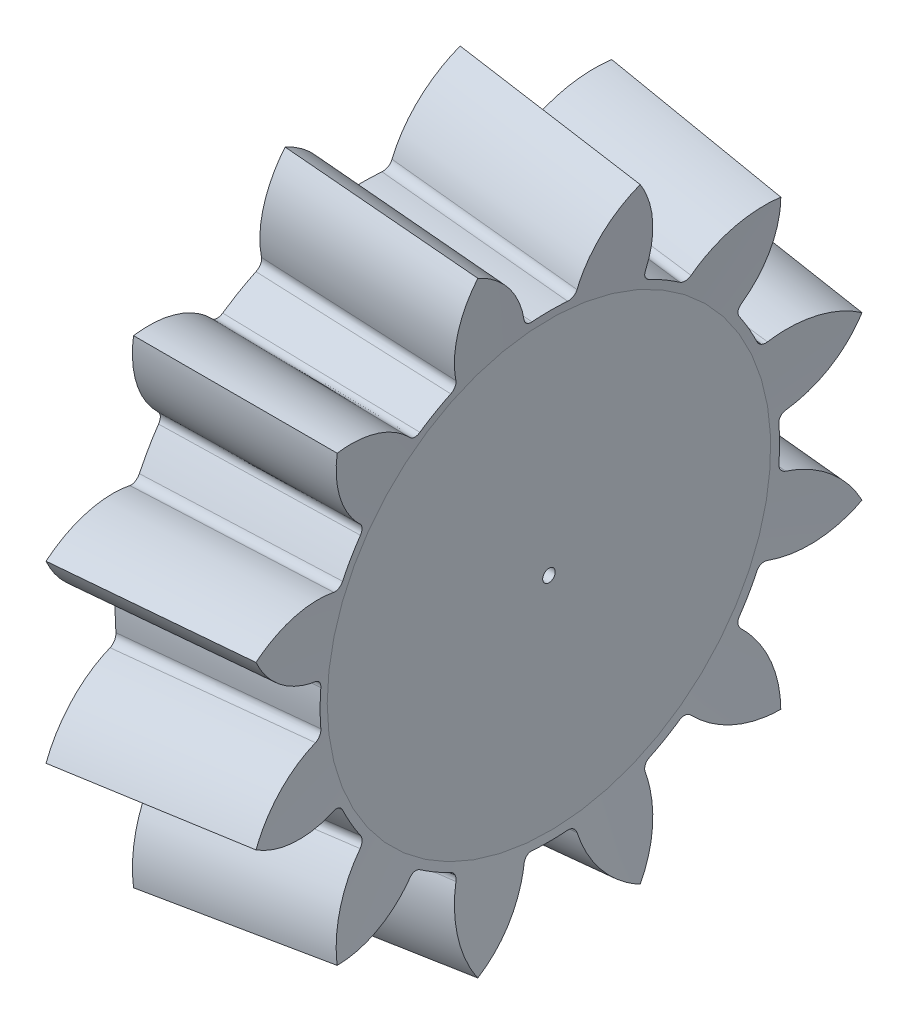
SolidWorks part; units mm, degrees
revolve "Base-Revolve" add sketch "BasProSke" angle 360 about L0
sketch "BasProSke" plane through (0, 0, 0) normal (0, 1, 0) x (1, 0, 0)
  line L0 (-10, 0) -> (60, 0) construction
  line L1 (0, 0) -> (0, 15.2645)
  line L2 (0, 0) -> (11.9508, 0)
  line L3 (11.9508, 0) -> (11.9508, 14.1609)
  line L4 (165.2984, 0) -> (-31.2241, 21.4388) construction
  line L5 (0, 15.2645) -> (0.7716, 22.3378)
  line L6 (165.2984, 0) -> (-7.6838, 23.4858) construction
  line L7 (165.2984, 0) -> (0, 15.2645) construction
  line L8 (0.7716, 22.3378) -> (12.6667, 20.7229)
  line L9 (12.6667, 20.7229) -> (11.9508, 14.1609)
  line L10 (0.2984, 18) -> (-11.6859, 18) construction
  dimension "Addendum" = 4.3636
  dimension "Pitch_rad" = 18
  dimension "Dedendum_plus" = 2.7518
  dimension "Face_wid" = 12
  dimension "Pitch_ang" = 6.226
  dimension "D1" = 30.5289
  dimension "D2" = 165.2984
  dimension "D3" = 165.9789
  dimension "D4" = 1.506
ref_plane "Plane1" through (0, 0, 0) normal (0, 0, 1) x (1, 0, 0)
ref_plane "Plane2" through (0, 0, 0) normal (0, 1, 0) x (1, 0, 0)
ref_plane "Plane3" through (0, 0, 0) normal (1, 0, 0) x (0, 0, -1)
sketch "HoldingSke" plane through (0, 0, 0) normal (0, 1, 0) x (1, 0, 0)
  line L0 (0, 0) -> (0.326, -0.0693)
  line L1 (-15, 0) -> (100, 0) construction
  line L2 (0, 0) -> (195.858, 55.667)
  line L3 (0, 0) -> (-11.863, 4.5341)
  line L4 (0, 0) -> (8.4473, 1.7955)
  line L5 (0, 0) -> (-9.3695, -3.4946)
  line L6 (0, 0) -> (-10.5278, -7.1032)
  line L7 (195.858, 55.667) -> (359.3705, 31.4336)
  line L8 (-76.2, 3) -> (-76.1, 3)
  line L9 (-71.009, 38.7566) -> (-53.1078, 45.2721)
  line L10 (-76.2, 71.12) -> (104.1128, 71.12)
  line L11 (0, 0) -> (-12, 0)
  line L12 (-76.2, 101.6) -> (-76.093, 101.6)
  line L13 (24.9733, 27.94) -> (52.9471, 28.6503)
  line L14 (24.9733, 27.94) -> (24.9743, 27.94)
  line L15 (24.9733, 27.94) -> (100.4124, 28.9058)
  line L16 (195.858, 55.667) -> (151.7007, -65.6542)
  circle A0 centre (0, 0) radius 0.4
  circle A1 centre (0, 0) radius 15.2645
  circle A2 centre (0, 0) radius 37.5
  circle A3 centre (0, 0) radius 0.4
  dimension "MHD" = 30.5289
  dimension "Hub_dia" = 75
  dimension "Bore" = 0.8
  dimension "MBD" = 0.8
  dimension "Num_teeth" = 12
  dimension "Pitch" = 0.3333
  dimension "Mounting_dist" = 10
  dimension "Show_teeth" = 12
  dimension "Thickness" = 12.7
  dimension "OAL" = 165.2985
  dimension "T_dim" = 0.1
  dimension "Ap" = 20
  dimension "H" = 19.05
  dimension "Pitch_radius" = 180.3128
  dimension "Width" = 12
  dimension "Backlash" = 0.107
  dimension "Addendum_fac" = 1.455
  dimension "Dedendum_fac" = 0.733
  dimension "Clearance_fac" = 0.188
  dimension "Dedendum_add" = 0.001
  dimension "Mating_teeth" = 110
  dimension "MnMD" = 165.2984
  dimension "Module" = 3
ref_plane "ToothPln" through (0.3858, 18.8011, 0) normal (-0.9941, 0.1084, 0) x (0, 0, -1)
ref_plane "ToothPln2" through (163.3544, -17.8205, 0) normal (-0.9941, 0.1084, 0) x (0, 0, 1)
sketch "TooCutSke" plane through (0.3858, 18.8011, 0) normal (-0.9941, 0.1084, 0) x (0, 0, -1)
  line L2 (0, 18.8059) -> (441.7526, -1629.8373) construction
  line L3 (0, 18.8059) -> (238.7007, -1753.2468) construction
  line L4 (0, -15.621) -> (0, 105.791) construction
  line L6 (-24.765, -3.5577) -> (21.082, -3.5577) construction
  line L7 (4.6587, 1.4192) -> (2.3833, 1.1127) construction
  arc A0 (-7.5403, -2.7227) -> (7.5403, -2.7227) centre (0, 18.8059) ccw
  arc A1 (-1.2274, 3.0551) -> (1.2274, 3.0551) centre (0, 18.8059) ccw
  circle A2 centre (0, 18.8059) radius 18 construction
  circle A3 centre (0, 18.8059) radius 16.9145 construction
  arc A4 (1.8196, 2.6281) -> (1.2274, 3.0551) centre (1.2712, 2.4918) ccw
  arc A5 (1.8196, 2.6281) -> (7.5403, -2.7227) centre (8.8069, 4.3651) ccw
  arc A6 (-7.5403, -2.7227) -> (-1.8196, 2.6281) centre (-8.8069, 4.3651) ccw
  arc A7 (-1.2274, 3.0551) -> (-1.8196, 2.6281) centre (-1.2712, 2.4918) ccw
  ellipse E0 centre (0, 18.6484) end of major axis (22.3378, 18.6484) minor radius 22.2061 construction
sketch "TooCutSke2" plane through (163.3544, -17.8205, 0) normal (-0.9941, 0.1084, 0) x (0, 0, 1)
  line L0 (0, 0) -> (0, 68.072) construction
  line L2 (21.082, 15.1744) -> (-20.32, 15.1744) construction
  circle A0 centre (0, 17.9262) radius 0.0127
  ellipse E1 centre (0, 0) end of major axis (-15.2645, 0) minor radius 15.1744 construction
  dimension "Dedendum_plus" = 2.7518
loft "ToothCut" cut profiles "TooCutSke2", "TooCutSke"
pattern_circular "TeethCuts" count 12 every 30 about axis through (-10, 0, 0) along (1, 0, 0) of "ToothCut"
sketch "HubSke" plane through (0, 0, 0) normal (-1, 0, 0) x (0, 0, 1)
  circle A0 centre (0, 0) radius 15.2645
  dimension "Diameter" = 30.5289
extrude "Hub" add sketch "HubSke" along normal blind 0.0001
sketch "BorSke" plane through (0, 0, 0) normal (1, 0, 0) x (0, 0, -1)
  circle A0 centre (0, 0) radius 0.4
  dimension "Diameter" = 0.8
extrude "Bore" cut sketch "BorSke" along normal mid plane 330.5969
sketch "KeySke" plane through (0, 0, 0) normal (1, 0, 0) x (0, 0, -1)
  line L0 (-0.05, 0) -> (-0.05, 0.5)
  line L1 (-0.05, 0.5) -> (0.05, 0.5)
  line L2 (0.05, 0.5) -> (0.05, 0)
  line L3 (0, 0) -> (0, 34) construction
  line L4 (-0.05, 0) -> (0.05, 0)
  dimension "Offset" = 0.5
extrude "Keyway" [suppressed] cut sketch "KeySke" along normal mid plane 330.5969
pattern_circular "Keyway2" [suppressed] count 2 every 90 about axis through (-10, 0, 0) along (1, 0, 0)
equation "' \"Module@HoldingSke\" = 6.35"
equation "' \"Num_teeth@HoldingSke\" = 12"
equation "' \"Mating_teeth@HoldingSke\" = 20"
equation "' \"Ap@HoldingSke\" =  20"
equation "' \"Ap@HoldingSke\" = 20"
equation "' \"Width@HoldingSke\" = 0.5 * 25.4"
equation "' \"Hub_dia@HoldingSke\"= 2 * 25.4"
equation "' \"Hub_dia@HoldingSke\" = 2 * 25.4"
equation "' \"Mounting_dist@HoldingSke\" = 3 * 25.4"
equation "' \"Bore@HoldingSke\" = 19"
equation "' \"T_dim@HoldingSke\" = 0.1 * 25.4"
equation "' \"Width@KeySke\" = 0.25 * 25.4"
equation "' \"Show_teeth@HoldingSke\" = 100"
equation "' \"Backlash@HoldingSke\" = 0.009 * 25.4"
equation "' \"Addendum_fac@HoldingSke\" = 1.0"
equation "' \"Dedendum_fac@HoldingSke\" = 1.188"
equation "' \"Dedendum_add@HoldingSke\" = 0.002 * 25.4"
equation "' \"Clearance_fac@HoldingSke\" = 0.188"
equation "\"Pitch@HoldingSke\" = 1 / \"Module@HoldingSke\""
equation "' \"Addendum_fac@HoldingSke\" = 0.54 + 0.46 / (\"Num_teeth@HoldingSke\" /  \"Mating_teeth@HoldingSke\" ) ^ 2"
equation " \"Addendum_fac@HoldingSke\" = 2 - (0.54 + 0.46 / (\"Mating_teeth@HoldingSke\" /  \"Num_teeth@HoldingSke\" ) ^ 2)"
equation "\"Dedendum_fac@HoldingSke\" = 2.188 - \"Addendum_fac@HoldingSke\""
equation "\"Pitch_rad@BasProSke\" = \"Num_teeth@HoldingSke\" / \"Pitch@HoldingSke\" / 2"
equation "\"Pitch_ang@BasProSke\" = atn(\"Num_teeth@HoldingSke\" / \"Mating_teeth@HoldingSke\") * (180 / 3.14159265)"
equation "\"Addendum@BasProSke\" = \"Addendum_fac@HoldingSke\" / \"Pitch@HoldingSke\""
equation "\"Dedendum_plus@BasProSke\" = (\"Dedendum_fac@HoldingSke\" / \"Pitch@HoldingSke\" + \"Dedendum_add@HoldingSke\") * 1.25"
equation "\"Face_wid@BasProSke\" = \"Width@HoldingSke\""
equation "\"Radius@TooCutSke\" = ((\"Num_teeth@HoldingSke\" + 2 * \"Addendum_fac@HoldingSke\") / \"Pitch@HoldingSke\" ) / 2"
equation "\"Overcut_dia@TooCutSke\" =  1.02 * (\"Num_teeth@HoldingSke\" + 2 * \"Addendum_fac@HoldingSke\") / \"Pitch@HoldingSke\""
equation "\"Pitch_dia@TooCutSke\" = \"Num_teeth@HoldingSke\" / \"Pitch@HoldingSke\""
equation "\"Base_dia@TooCutSke\" = \"Num_teeth@HoldingSke\" / \"Pitch@HoldingSke\" * cos((\"Ap@HoldingSke\"  * 3.14159265 / 180))"
equation "'  \"Root_dia@TooCutSke\" =  (\"Num_teeth@HoldingSke\" + 2) / \"Pitch@HoldingSke\" - 2 * (\"Addendum_fac@HoldingSke\" + \"Dedendum_fac@HoldingSke\") / \"Pitch@HoldingSke\" - \"Dedendum_add@HoldingSke\" * 2"
equation "'  \"Root_dia@TooCutSke\" = (\"Num_teeth@HoldingSke\" + 2) / \"Pitch@HoldingSke\" - 2 * (\"Addendum_fac@HoldingSke\" + \"Dedendum_fac@HoldingSke\") / \"Pitch@HoldingSke\" - \"Dedendum_add@HoldingSke\" * 2"
equation "\"Root_dia@TooCutSke\" =  \"Num_teeth@HoldingSke\" / \"Pitch@HoldingSke\" -  2 * \"Dedendum_fac@HoldingSke\" / \"Pitch@HoldingSke\" - \"Dedendum_add@HoldingSke\" * 2"
equation "\"Half_ang@TooCutSke\" = 180 / \"Num_teeth@HoldingSke\""
equation "\"Half_CT@TooCutSke\" = \"Num_teeth@HoldingSke\" / \"Pitch@HoldingSke\" * sin((3.14159265 / 2 / \"Num_teeth@HoldingSke\")) / 2 - 2 * \"Backlash@HoldingSke\" / 4"
equation "\"Flank_rad@TooCutSke\" = \"Num_teeth@HoldingSke\" / \"Pitch@HoldingSke\" / 5"
equation "\"Root_fillet@TooCutSke\" = \"Clearance_fac@HoldingSke\" / \"Pitch@HoldingSke\" + \"Dedendum_add@HoldingSke\""
equation "\"Offset@ToothPln2\"  = \"Num_teeth@HoldingSke\" / \"Pitch@HoldingSke\" / 2 / sin(atn(\"Num_teeth@HoldingSke\" / \"Mating_teeth@HoldingSke\"))"
equation "\"Dedendum_plus@TooCutSke2\" = \"Dedendum_plus@BasProSke\""
equation "\"MHD@HoldingSke\" = \"Num_teeth@HoldingSke\" / \"Pitch@HoldingSke\" - 2 * \"Dedendum_plus@BasProSke\" * cos(atn(\"Num_teeth@HoldingSke\" / \"Mating_teeth@HoldingSke\"))"
equation "\"MBD@HoldingSke\" = \"Num_teeth@HoldingSke\" / \"Pitch@HoldingSke\" - 2 * \"Dedendum_plus@BasProSke\" * cos(atn(\"Num_teeth@HoldingSke\" / \"Mating_teeth@HoldingSke\")) - 0.002 * 25.4"
equation "\"MnMD@HoldingSke\" =  \"Num_teeth@HoldingSke\" / \"Pitch@HoldingSke\" / 2 / (\"Num_teeth@HoldingSke\" / \"Mating_teeth@HoldingSke\") + \"Dedendum_plus@BasProSke\" * sin(atn(\"Num_teeth@HoldingSke\" / \"Mating_teeth@HoldingSke\"))"
equation "\"OAL@HoldingSke\" = \"MnMD@HoldingSke\""
equation "\"MHD@HoldingSke\" = ((sgn( \"MHD@HoldingSke\" - \"Hub_dia@HoldingSke\" )-1)*( \"MHD@HoldingSke\" - \"Hub_dia@HoldingSke\" ))/-2+ \"Hub_dia@HoldingSke\""
equation "\"MBD@HoldingSke\" = ((sgn( \"MBD@HoldingSke\" - \"Bore@HoldingSke\" )-1)*( \"MBD@HoldingSke\" - \"Bore@HoldingSke\" ))/-2+ \"Bore@HoldingSke\""
equation "\"Face_wid@BasProSke\" = ((sgn( \"Face_wid@BasProSke\" - \"Offset@ToothPln2\" * 0.9)-1)*( \"Face_wid@BasProSke\" - \"Offset@ToothPln2\" * 0.9))/-2+ \"Offset@ToothPln2\" * 0.9"
equation "\"OAL@HoldingSke\" = ((sgn( \"OAL@HoldingSke\" - \"Mounting_dist@HoldingSke\" )+1)*( \"OAL@HoldingSke\" - \"Mounting_dist@HoldingSke\" ))/2 + \"Mounting_dist@HoldingSke\" + 0.000002 * 25.4"
equation "\"Num_teeth@TeethCuts\" = int( \"Show_teeth@HoldingSke\" ) + 1"
equation "\"Num_teeth@TeethCuts\" = ((sgn( \"Num_teeth@TeethCuts\" - \"Num_teeth@HoldingSke\" )-1)*( \"Num_teeth@TeethCuts\" - \"Num_teeth@HoldingSke\" ))/-2+ \"Num_teeth@HoldingSke\""
equation "\"Num_teeth@TeethCuts\" = ((sgn( \"Num_teeth@TeethCuts\" - 2.0)+1)*( \"Num_teeth@TeethCuts\" - 2.0))/2 +2.0"
equation "\"Angle@TeethCuts\" = 360.0 / \"Num_teeth@HoldingSke\""
equation "\"Diameter@HubSke\" = \"MHD@HoldingSke\""
equation "\"Length@Hub\" = \"OAL@HoldingSke\" - \"MnMD@HoldingSke\" + 0.000002 * 25.4"
equation "\"Diameter@BorSke\" = \"MBD@HoldingSke\""
equation "\"D1@Bore\" = \"OAL@HoldingSke\" * 2.0"
equation "\"D1@Keyway\" = \"OAL@HoldingSke\" * 2.0"
equation "\"Offset@KeySke\" = \"T_dim@HoldingSke\" + \"MBD@HoldingSke\" / 2.0"
